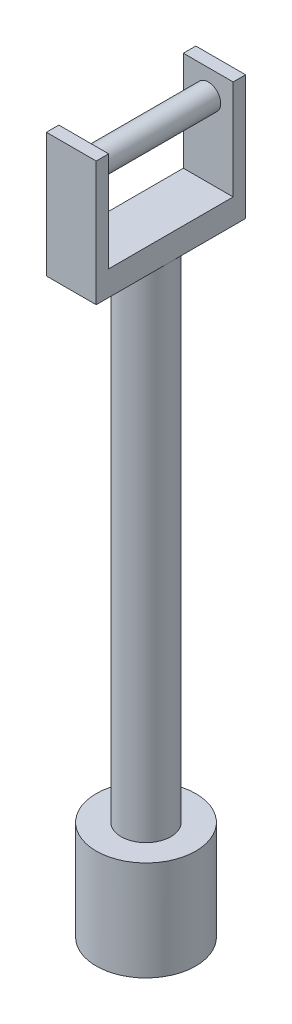
SolidWorks part; units mm, degrees
ref_plane "Front Plane" through (0, 0, 0) normal (0, 0, 1) x (1, 0, 0)
ref_plane "Top Plane" through (0, 0, 0) normal (0, 1, 0) x (1, 0, 0)
ref_plane "Right Plane" through (0, 0, 0) normal (1, 0, 0) x (0, 0, -1)
sketch "Sketch2" plane through (0, 0, 0) normal (0, 1, 0) x (1, 0, 0)
  circle A0 centre (0, 0) radius 25.4
  dimension "D1" = 50.8
extrude "Boss-Extrude1" add sketch "Sketch2" along normal blind 25.4
sketch "Sketch3" plane through (0, 25.4, 0) normal (0, 1, 0) x (1, 0, 0)
  circle A0 centre (0, 0) radius 12.7
  dimension "D1" = 25.4
extrude "Boss-Extrude2" add sketch "Sketch3" along normal blind 254
sketch "Sketch4" plane through (0, 279.4, 0) normal (0, 1, 0) x (1, 0, 0)
  line L1 (-12.7, 38.1) -> (12.7, 38.1)
  line L2 (-12.7, 38.1) -> (-12.7, -38.1)
  line L3 (-12.7, -38.1) -> (12.7, -38.1)
  line L4 (12.7, 38.1) -> (12.7, -38.1)
  line L5 (-12.7, 38.1) -> (12.7, -38.1) construction
  line L6 (-12.7, -38.1) -> (12.7, 38.1) construction
  point P0 (0, 0)
  dimension "D1" = 76.2
  dimension "D2" = 25.4
extrude "Boss-Extrude3" add sketch "Sketch4" along normal blind 12.7
sketch "Sketch5" plane through (0, 292.1, 0) normal (0, 1, 0) x (1, 0, 0)
  line L0 (12.7, -38.1) -> (12.7, 38.1) construction
  line L1 (-12.7, 38.1) -> (12.7, 38.1)
  line L2 (-12.7, 38.1) -> (-12.7, 31.75)
  line L3 (-12.7, 31.75) -> (12.7, 31.75)
  line L4 (12.7, 38.1) -> (12.7, 31.75)
  line L6 (-12.7, -38.1) -> (12.7, -38.1)
  line L7 (-12.7, -38.1) -> (-12.7, -31.75)
  line L8 (-12.7, -31.75) -> (12.7, -31.75)
  line L9 (12.7, -38.1) -> (12.7, -31.75)
  dimension "D1" = 6.35
  dimension "D2" = 6.35
extrude "Boss-Extrude4" add sketch "Sketch5" along normal blind 50.8
sketch "Sketch6" plane through (0, 0, 38.1) normal (0, 0, 1) x (1, 0, 0)
  line L0 (-12.7, 342.9) -> (-12.7, 330.2)
  line L1 (-12.7, 342.9) -> (-12.7, 279.4) construction
  line L2 (-12.7, 330.2) -> (12.7, 330.2)
  line L3 (12.7, 342.9) -> (12.7, 279.4) construction
  circle A0 centre (0, 330.2) radius 6.35
  dimension "D2" = 12.7
  dimension "D1" = 12.7
extrude "Boss-Extrude5" add sketch "Sketch6" against normal up to surface (69.85 mm away) contours A0 up to face at (0, 317.5, -31.75)
sketch "Sketch7" plane through (0, 0, 0) normal (0, -1, 0) x (1, 0, 0)
  circle A0 centre (0, 0) radius 25.4
extrude "Boss-Extrude6" add sketch "Sketch7" along normal blind 25.4
